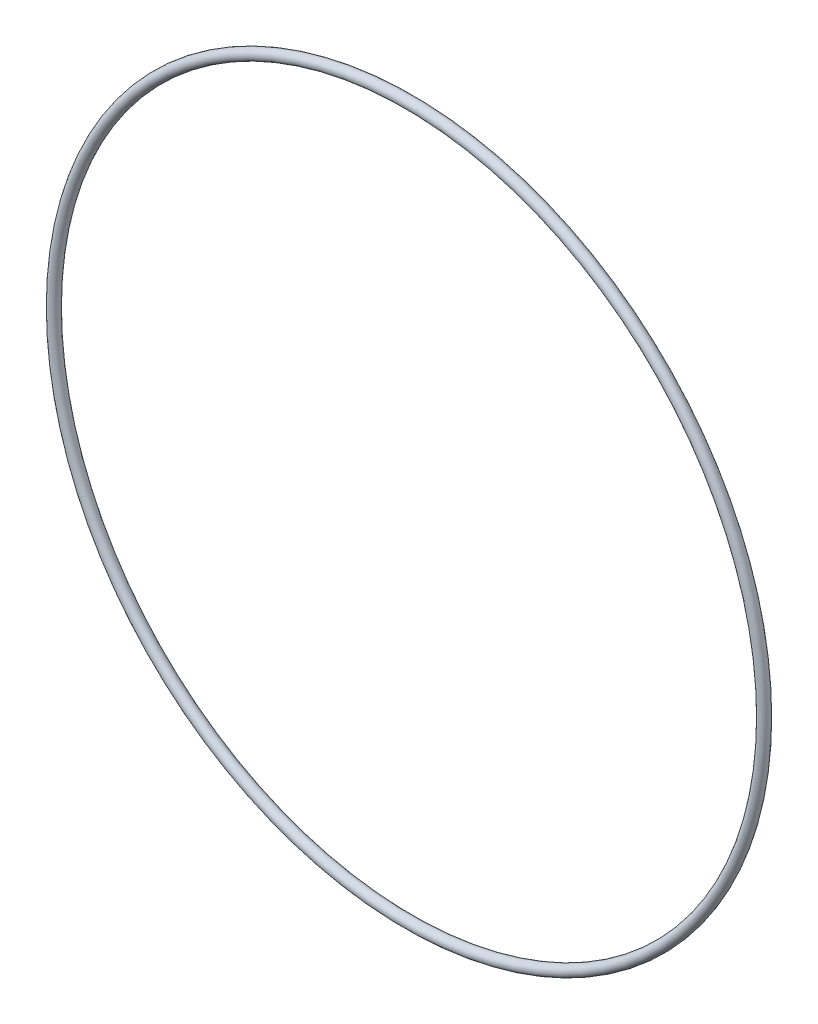
SolidWorks part; units mm, degrees
material "Rubber"
ref_plane "Front" through (0, 0, 0) normal (0, 0, 1) x (1, 0, 0)
ref_plane "Top" through (0, 0, 0) normal (0, 1, 0) x (1, 0, 0)
ref_plane "Right" through (0, 0, 0) normal (1, 0, 0) x (0, 0, -1)
sketch "Sketch1" plane through (0, 0, 0) normal (1, 0, 0) x (0, -1, 0)
  line L0 (0, -1.3081) -> (0, 1.3081) construction
  line L2 (-96.9937, 0) -> (96.9937, 0) construction
  line L3 (-85.5599, 0) -> (85.5599, 0) construction
  circle A0 centre (86.868, 0) radius 1.3081
  point P9 (85.5599, 0)
  point P10 (88.1761, 0)
  point P13 (86.868, 1.3081)
  point P14 (86.868, -1.3081)
  dimension "Width" = 2.6162
  dimension "ID" = 171.1198
revolve "Revolve1" add sketch "Sketch1" angle 360 about L0
